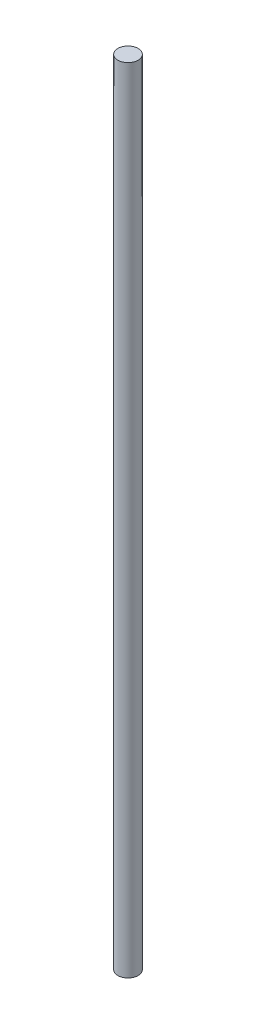
SolidWorks part; units mm, degrees
ref_plane "Ön Düzlem" through (0, 0, 0) normal (0, 0, 1) x (1, 0, 0)
ref_plane "Üst Düzlem" through (0, 0, 0) normal (0, 1, 0) x (1, 0, 0)
ref_plane "Sağ Düzlem" through (0, 0, 0) normal (1, 0, 0) x (0, 0, -1)
sketch "Çizim1" plane through (0, 0, 0) normal (0, 1, 0) x (1, 0, 0)
  circle A0 centre (0, 0) radius 5
  dimension "D1" = 10
extrude "Yükseklik-Ekstrüzyon1" add sketch "Çizim1" along normal blind 390
sketch "Çizim10" plane through (0, 390, 0) normal (0, 1, 0) x (1, 0, 0)
  line L0 (0, 0) -> (5, 0)
  circle A0 centre (0, 0) radius 5 construction
ref_plane "Düzlem3" through (5, 0, 0) normal (1, 0, 0) x (0, 0, -1)
sketch "Çizim11" plane through (5, 0, 0) normal (1, 0, 0) x (0, 0, -1)
  line L0 (0, 390) -> (0, 0) construction
  line L1 (5, 390) -> (-5, 390) construction
  line L2 (-4.7623, 195) -> (5, 195)
  line L3 (5, 0) -> (5, 390) construction
  point P5 (0, 195)
